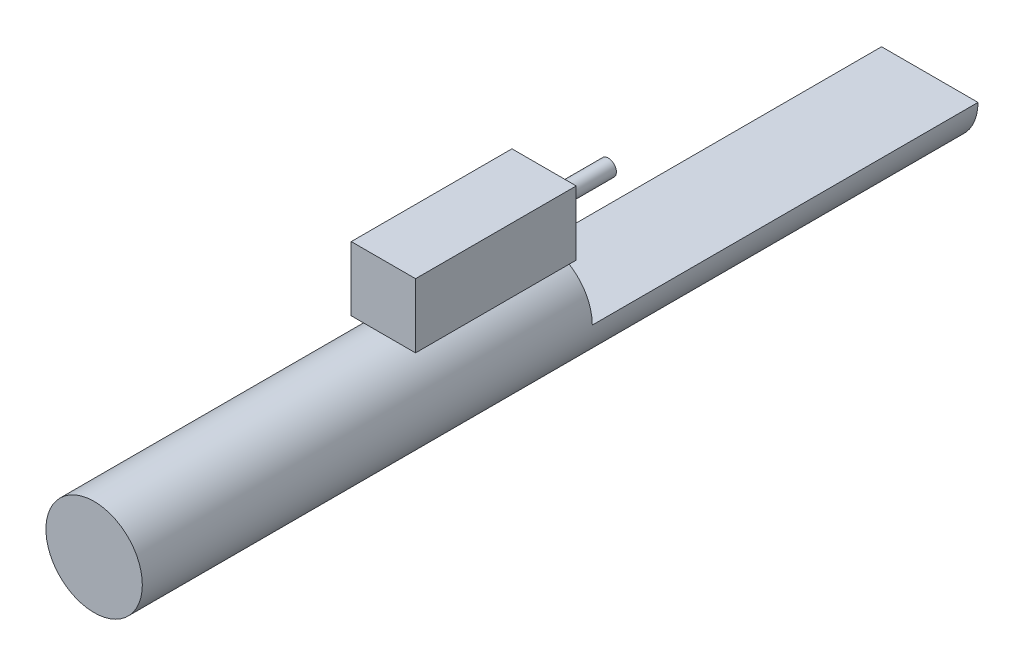
SolidWorks part; units mm, degrees
ref_plane "前基準面" through (0, 0, 0) normal (0, 0, 1) x (1, 0, 0)
ref_plane "上基準面" through (0, 0, 0) normal (0, 1, 0) x (1, 0, 0)
ref_plane "右基準面" through (0, 0, 0) normal (1, 0, 0) x (0, 0, -1)
sketch "草圖1" plane through (0, 0, 0) normal (0, 0, 1) x (1, 0, 0)
  circle A0 centre (0, 0) radius 7.5
  dimension "D1" = 15
extrude "填料-伸長1" add sketch "草圖1" along normal blind 70
ref_plane "平面1" through (0, 0, 0) normal (0, 0, -1) x (-1, 0, 0)
sketch "草圖2" plane through (0, 0, 0) normal (0, 0, -1) x (-1, 0, 0)
  line L0 (-7.5, 0) -> (7.5, 0)
  circle A0 centre (0, 0) radius 7.5 construction
  arc A1 (-7.5, 0) -> (7.5, 0) centre (0, 0) ccw
extrude "填料-伸長2" add sketch "草圖2" along normal blind 60
ref_plane "平面2" through (0, 7.5, 0) normal (0, 1, 0) x (1, 0, 0)
sketch "草圖4" plane through (0, 7.5, 0) normal (0, 1, 0) x (1, 0, 0)
  line L0 (4.125, 0) -> (-4.125, 0) construction
  line L1 (-5, 0) -> (5, 0)
  line L2 (-5, 0) -> (-5, -25)
  line L3 (-5, -25) -> (5, -25)
  line L4 (5, 0) -> (5, -25)
  line L5 (0, 0) -> (0, -44.7248) construction
  dimension "D1" = 0
  dimension "D2" = 25
  dimension "D3" = 10
  dimension "D4" = 5
extrude "填料-伸長3" add sketch "草圖4" along normal blind 10 separate body
ref_plane "平面3" through (0, 0, 0) normal (0, 0, -1) x (-1, 0, 0)
sketch "草圖5" plane through (0, 0, 0) normal (0, 0, -1) x (-1, 0, 0)
  line L0 (0, 17.5) -> (0, 7.5) construction
  line L1 (-5, 17.5) -> (5, 17.5) construction
  line L2 (8.25, 7.5) -> (-8.25, 7.5) construction
  circle A0 centre (0, 12.5) radius 1.25
  dimension "D1" = 2.5
extrude "填料-伸長4" add sketch "草圖5" along normal blind 10
